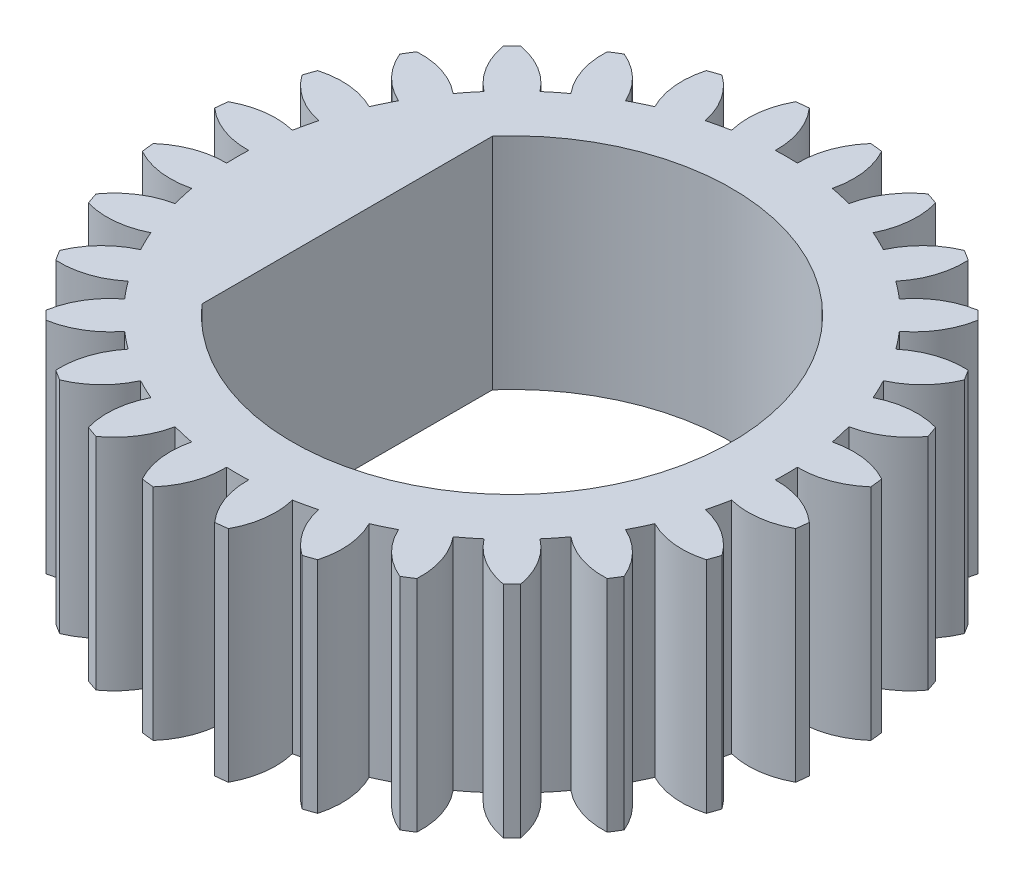
SolidWorks part; units mm, degrees
ref_plane "Front Plane" through (0, 0, 0) normal (0, 0, 1) x (1, 0, 0)
ref_plane "Top Plane" through (0, 0, 0) normal (0, 1, 0) x (1, 0, 0)
ref_plane "Right Plane" through (0, 0, 0) normal (1, 0, 0) x (0, 0, -1)
sketch "Sketch1" plane through (0, 0, 0) normal (0, 1, 0) x (1, 0, 0)
  line L0 (0, 0) -> (0, 1) construction
  line L1 (0, 1.5) -> (0, 2.7903) construction
  line L2 (0, 0) -> (-0.75, 0) construction
  line L3 (-0.75, 0) -> (-0.75, 0.6614)
  line L4 (-0.75, 0) -> (-0.75, -0.6614)
  arc A0 (-0.75, -0.6614) -> (-0.75, 0.6614) centre (0, 0) ccw
  arc A1 (0.1958, 1.4872) -> (0.14, 1.4935) centre (0, 0) ccw
  arc A2 (-0.9453, 0.8178) -> (-1.0077, 0.7396) centre (0, 0) ccw construction
  arc A3 (0.05, 1.249) -> (0.14, 1.4935) centre (0.4074, 1.2562) cw
  arc A4 (-0.05, 1.249) -> (-0.14, 1.4935) centre (-0.4074, 1.2562) ccw
  arc A5 (-0.05, 1.249) -> (0.05, 1.249) centre (0, 0) cw
  arc A6 (0.2292, 1.2288) -> (0.1958, 1.4872) centre (-0.1176, 1.3154) ccw
  arc A7 (0.3267, 1.2066) -> (0.4688, 1.4249) centre (0.6767, 1.1341) cw
  arc A8 (0.4969, 1.147) -> (0.5218, 1.4063) centre (0.178, 1.3086) ccw
  arc A9 (0.587, 1.1036) -> (0.7741, 1.2848) centre (0.9121, 0.9551) cw
  arc A10 (0.7396, 1.0077) -> (0.8217, 1.2549) centre (0.4648, 1.2361) ccw
  arc A11 (0.8178, 0.9453) -> (1.0406, 1.0803) centre (1.1017, 0.7282) cw
  arc A12 (0.9453, 0.8178) -> (1.0803, 1.0406) centre (0.7282, 1.1017) ccw
  arc A13 (1.0077, 0.7396) -> (1.2549, 0.8217) centre (1.2361, 0.4648) cw
  arc A14 (1.1036, 0.587) -> (1.2848, 0.7741) centre (0.9551, 0.9121) ccw
  arc A15 (1.147, 0.4969) -> (1.4063, 0.5218) centre (1.3086, 0.178) cw
  arc A16 (1.2066, 0.3267) -> (1.4249, 0.4688) centre (1.1341, 0.6767) ccw
  arc A17 (1.2288, 0.2292) -> (1.4872, 0.1958) centre (1.3154, -0.1176) cw
  arc A18 (1.249, 0.05) -> (1.4935, 0.14) centre (1.2562, 0.4074) ccw
  arc A19 (1.249, -0.05) -> (1.4935, -0.14) centre (1.2562, -0.4074) cw
  arc A20 (1.2288, -0.2292) -> (1.4872, -0.1958) centre (1.3154, 0.1176) ccw
  arc A21 (1.2066, -0.3267) -> (1.4249, -0.4688) centre (1.1341, -0.6767) cw
  arc A22 (1.147, -0.4969) -> (1.4063, -0.5218) centre (1.3086, -0.178) ccw
  arc A23 (1.1036, -0.587) -> (1.2848, -0.7741) centre (0.9551, -0.9121) cw
  arc A24 (1.0077, -0.7396) -> (1.2549, -0.8217) centre (1.2361, -0.4648) ccw
  arc A25 (0.9453, -0.8178) -> (1.0803, -1.0406) centre (0.7282, -1.1017) cw
  arc A26 (0.8178, -0.9453) -> (1.0406, -1.0803) centre (1.1017, -0.7282) ccw
  arc A27 (0.7396, -1.0077) -> (0.8217, -1.2549) centre (0.4648, -1.2361) cw
  arc A28 (0.587, -1.1036) -> (0.7741, -1.2848) centre (0.9121, -0.9551) ccw
  arc A29 (0.4969, -1.147) -> (0.5218, -1.4063) centre (0.178, -1.3086) cw
  arc A30 (0.3267, -1.2066) -> (0.4688, -1.4249) centre (0.6767, -1.1341) ccw
  arc A31 (0.2292, -1.2288) -> (0.1958, -1.4872) centre (-0.1176, -1.3154) cw
  arc A32 (0.05, -1.249) -> (0.14, -1.4935) centre (0.4074, -1.2562) ccw
  arc A33 (-0.05, -1.249) -> (-0.14, -1.4935) centre (-0.4074, -1.2562) cw
  arc A34 (-0.2292, -1.2288) -> (-0.1958, -1.4872) centre (0.1176, -1.3154) ccw
  arc A35 (-0.3267, -1.2066) -> (-0.4688, -1.4249) centre (-0.6767, -1.1341) cw
  arc A36 (-0.4969, -1.147) -> (-0.5218, -1.4063) centre (-0.178, -1.3086) ccw
  arc A37 (-0.587, -1.1036) -> (-0.7741, -1.2848) centre (-0.9121, -0.9551) cw
  arc A38 (-0.7396, -1.0077) -> (-0.8217, -1.2549) centre (-0.4648, -1.2361) ccw
  arc A39 (-0.8178, -0.9453) -> (-1.0406, -1.0803) centre (-1.1017, -0.7282) cw
  arc A40 (-0.9453, -0.8178) -> (-1.0803, -1.0406) centre (-0.7282, -1.1017) ccw
  arc A41 (-1.0077, -0.7396) -> (-1.2549, -0.8217) centre (-1.2361, -0.4648) cw
  arc A42 (-1.1036, -0.587) -> (-1.2848, -0.7741) centre (-0.9551, -0.9121) ccw
  arc A43 (-1.147, -0.4969) -> (-1.4063, -0.5218) centre (-1.3086, -0.178) cw
  arc A44 (-1.2066, -0.3267) -> (-1.4249, -0.4688) centre (-1.1341, -0.6767) ccw
  arc A45 (-1.2288, -0.2292) -> (-1.4872, -0.1958) centre (-1.3154, 0.1176) cw
  arc A46 (-1.249, -0.05) -> (-1.4935, -0.14) centre (-1.2562, -0.4074) ccw
  arc A47 (-1.249, 0.05) -> (-1.4935, 0.14) centre (-1.2562, 0.4074) cw
  arc A48 (-1.2288, 0.2292) -> (-1.4872, 0.1958) centre (-1.3154, -0.1176) ccw
  arc A49 (-1.2066, 0.3267) -> (-1.4249, 0.4688) centre (-1.1341, 0.6767) cw
  arc A50 (-1.147, 0.4969) -> (-1.4063, 0.5218) centre (-1.3086, 0.178) ccw
  arc A51 (-1.1036, 0.587) -> (-1.2848, 0.7741) centre (-0.9551, 0.9121) cw
  arc A52 (-1.0077, 0.7396) -> (-1.2549, 0.8217) centre (-1.2361, 0.4648) ccw
  arc A53 (-0.9453, 0.8178) -> (-1.0803, 1.0406) centre (-0.7282, 1.1017) cw
  arc A54 (-0.8178, 0.9453) -> (-1.0406, 1.0803) centre (-1.1017, 0.7282) ccw
  arc A55 (-0.7396, 1.0077) -> (-0.8217, 1.2549) centre (-0.4648, 1.2361) cw
  arc A56 (-0.587, 1.1036) -> (-0.7741, 1.2848) centre (-0.9121, 0.9551) ccw
  arc A57 (-0.4969, 1.147) -> (-0.5218, 1.4063) centre (-0.178, 1.3086) cw
  arc A58 (-0.3267, 1.2066) -> (-0.4688, 1.4249) centre (-0.6767, 1.1341) ccw
  arc A59 (-0.2292, 1.2288) -> (-0.1958, 1.4872) centre (0.1176, 1.3154) cw
  arc A60 (-0.14, 1.4935) -> (-0.1958, 1.4872) centre (0, 0) ccw
  arc A61 (-0.4688, 1.4249) -> (-0.5218, 1.4063) centre (0, 0) ccw
  arc A62 (-0.7741, 1.2848) -> (-0.8217, 1.2549) centre (0, 0) ccw
  arc A63 (-1.0406, 1.0803) -> (-1.0803, 1.0406) centre (0, 0) ccw
  arc A64 (-1.2549, 0.8217) -> (-1.2848, 0.7741) centre (0, 0) ccw
  arc A65 (-1.4063, 0.5218) -> (-1.4249, 0.4688) centre (0, 0) ccw
  arc A66 (-1.4872, 0.1958) -> (-1.4935, 0.14) centre (0, 0) ccw
  arc A67 (-1.4935, -0.14) -> (-1.4872, -0.1958) centre (0, 0) ccw
  arc A68 (-1.4249, -0.4688) -> (-1.4063, -0.5218) centre (0, 0) ccw
  arc A69 (-1.2848, -0.7741) -> (-1.2549, -0.8217) centre (0, 0) ccw
  arc A70 (-1.0803, -1.0406) -> (-1.0406, -1.0803) centre (0, 0) ccw
  arc A71 (-0.8217, -1.2549) -> (-0.7741, -1.2848) centre (0, 0) ccw
  arc A72 (-0.5218, -1.4063) -> (-0.4688, -1.4249) centre (0, 0) ccw
  arc A73 (-0.1958, -1.4872) -> (-0.14, -1.4935) centre (0, 0) ccw
  arc A74 (0.14, -1.4935) -> (0.1958, -1.4872) centre (0, 0) ccw
  arc A75 (0.4688, -1.4249) -> (0.5218, -1.4063) centre (0, 0) ccw
  arc A76 (0.7741, -1.2848) -> (0.8217, -1.2549) centre (0, 0) ccw
  arc A77 (1.0406, -1.0803) -> (1.0803, -1.0406) centre (0, 0) ccw
  arc A78 (1.2549, -0.8217) -> (1.2848, -0.7741) centre (0, 0) ccw
  arc A79 (1.4063, -0.5218) -> (1.4249, -0.4688) centre (0, 0) ccw
  arc A80 (1.4872, -0.1958) -> (1.4935, -0.14) centre (0, 0) ccw
  arc A81 (1.4935, 0.14) -> (1.4872, 0.1958) centre (0, 0) ccw
  arc A82 (1.4249, 0.4688) -> (1.4063, 0.5218) centre (0, 0) ccw
  arc A83 (1.2848, 0.7741) -> (1.2549, 0.8217) centre (0, 0) ccw
  arc A84 (1.0803, 1.0406) -> (1.0406, 1.0803) centre (0, 0) ccw
  arc A85 (0.8217, 1.2549) -> (0.7741, 1.2848) centre (0, 0) ccw
  arc A86 (0.5218, 1.4063) -> (0.4688, 1.4249) centre (0, 0) ccw
  arc A87 (-1.1036, 0.587) -> (-1.147, 0.4969) centre (0, 0) ccw construction
  arc A88 (-0.9453, 0.8178) -> (-1.0077, 0.7396) centre (0, 0) ccw
  arc A89 (-1.1036, 0.587) -> (-1.147, 0.4969) centre (0, 0) ccw
  arc A90 (-1.2066, 0.3267) -> (-1.2288, 0.2292) centre (0, 0) ccw construction
  arc A91 (-1.2066, 0.3267) -> (-1.2288, 0.2292) centre (0, 0) ccw
  arc A92 (-1.249, 0.05) -> (-1.249, -0.05) centre (0, 0) ccw construction
  arc A93 (-1.249, 0.05) -> (-1.249, -0.05) centre (0, 0) ccw
  arc A94 (-1.2288, -0.2292) -> (-1.2066, -0.3267) centre (0, 0) ccw construction
  arc A95 (-1.2288, -0.2292) -> (-1.2066, -0.3267) centre (0, 0) ccw
  arc A96 (-1.147, -0.4969) -> (-1.1036, -0.587) centre (0, 0) ccw construction
  arc A97 (-1.147, -0.4969) -> (-1.1036, -0.587) centre (0, 0) ccw
  arc A98 (-1.0077, -0.7396) -> (-0.9453, -0.8178) centre (0, 0) ccw construction
  arc A99 (-1.0077, -0.7396) -> (-0.9453, -0.8178) centre (0, 0) ccw
  arc A100 (-0.8178, -0.9453) -> (-0.7396, -1.0077) centre (0, 0) ccw construction
  arc A101 (-0.8178, -0.9453) -> (-0.7396, -1.0077) centre (0, 0) ccw
  arc A102 (-0.587, -1.1036) -> (-0.4969, -1.147) centre (0, 0) ccw construction
  arc A103 (-0.587, -1.1036) -> (-0.4969, -1.147) centre (0, 0) ccw
  arc A104 (-0.3267, -1.2066) -> (-0.2292, -1.2288) centre (0, 0) ccw construction
  arc A105 (-0.3267, -1.2066) -> (-0.2292, -1.2288) centre (0, 0) ccw
  arc A106 (-0.05, -1.249) -> (0.05, -1.249) centre (0, 0) ccw construction
  arc A107 (-0.05, -1.249) -> (0.05, -1.249) centre (0, 0) ccw
  arc A108 (0.2292, -1.2288) -> (0.3267, -1.2066) centre (0, 0) ccw construction
  arc A109 (0.2292, -1.2288) -> (0.3267, -1.2066) centre (0, 0) ccw
  arc A110 (0.4969, -1.147) -> (0.587, -1.1036) centre (0, 0) ccw construction
  arc A111 (0.4969, -1.147) -> (0.587, -1.1036) centre (0, 0) ccw
  arc A112 (0.7396, -1.0077) -> (0.8178, -0.9453) centre (0, 0) ccw construction
  arc A113 (0.7396, -1.0077) -> (0.8178, -0.9453) centre (0, 0) ccw
  arc A114 (0.9453, -0.8178) -> (1.0077, -0.7396) centre (0, 0) ccw construction
  arc A115 (0.9453, -0.8178) -> (1.0077, -0.7396) centre (0, 0) ccw
  arc A116 (1.1036, -0.587) -> (1.147, -0.4969) centre (0, 0) ccw construction
  arc A117 (1.1036, -0.587) -> (1.147, -0.4969) centre (0, 0) ccw
  arc A118 (1.2066, -0.3267) -> (1.2288, -0.2292) centre (0, 0) ccw construction
  arc A119 (1.2066, -0.3267) -> (1.2288, -0.2292) centre (0, 0) ccw
  arc A120 (1.249, -0.05) -> (1.249, 0.05) centre (0, 0) ccw construction
  arc A121 (1.249, -0.05) -> (1.249, 0.05) centre (0, 0) ccw
  arc A122 (1.2288, 0.2292) -> (1.2066, 0.3267) centre (0, 0) ccw construction
  arc A123 (1.2288, 0.2292) -> (1.2066, 0.3267) centre (0, 0) ccw
  arc A124 (1.147, 0.4969) -> (1.1036, 0.587) centre (0, 0) ccw construction
  arc A125 (1.147, 0.4969) -> (1.1036, 0.587) centre (0, 0) ccw
  arc A126 (1.0077, 0.7396) -> (0.9453, 0.8178) centre (0, 0) ccw construction
  arc A127 (1.0077, 0.7396) -> (0.9453, 0.8178) centre (0, 0) ccw
  arc A128 (0.8178, 0.9453) -> (0.7396, 1.0077) centre (0, 0) ccw construction
  arc A129 (0.8178, 0.9453) -> (0.7396, 1.0077) centre (0, 0) ccw
  arc A130 (0.587, 1.1036) -> (0.4969, 1.147) centre (0, 0) ccw construction
  arc A131 (0.587, 1.1036) -> (0.4969, 1.147) centre (0, 0) ccw
  arc A132 (-0.7396, 1.0077) -> (-0.8178, 0.9453) centre (0, 0) ccw construction
  arc A133 (-0.7396, 1.0077) -> (-0.8178, 0.9453) centre (0, 0) ccw
  arc A134 (-0.4969, 1.147) -> (-0.587, 1.1036) centre (0, 0) ccw construction
  arc A135 (-0.4969, 1.147) -> (-0.587, 1.1036) centre (0, 0) ccw
  arc A136 (-0.2292, 1.2288) -> (-0.3267, 1.2066) centre (0, 0) ccw construction
  arc A137 (-0.2292, 1.2288) -> (-0.3267, 1.2066) centre (0, 0) ccw
  arc A138 (0.05, 1.249) -> (-0.05, 1.249) centre (0, 0) ccw construction
  arc A139 (0.05, 1.249) -> (-0.05, 1.249) centre (0, 0) ccw
  arc A140 (0.3267, 1.2066) -> (0.2292, 1.2288) centre (0, 0) ccw construction
  arc A141 (0.3267, 1.2066) -> (0.2292, 1.2288) centre (0, 0) ccw
  point P159 (0, 0)
  dimension "D1" = 2
  dimension "D2" = 3
  dimension "D3" = 2.5
  dimension "D8" = 1.25
  dimension "D4" = 0.05
  dimension "D5" = 0.14
  dimension "D7" = 0.2445
  dimension "D9" = 0.75
  dimension "D6" = 28
extrude "Boss-Extrude1" add sketch "Sketch1" along normal blind 1 contours A7 A141 A6 A1 A3 A5 A4 A60 A59 A137 A58 A61 A57 A135 A56 A62 A55 A133 A54 A63 A53 A88 A52 A64 A51 A89 A50 A65 A49 A91 A48 A66 A47 A93 A46 A67 A45 A95 A44 A68 A43 A97 A42 A69 A41 A99 A40 A70 A39 A101 A38 | A0
scale "Scale1" bodies to scale 101 scale about origin uniform scaling yes scale factor 2
